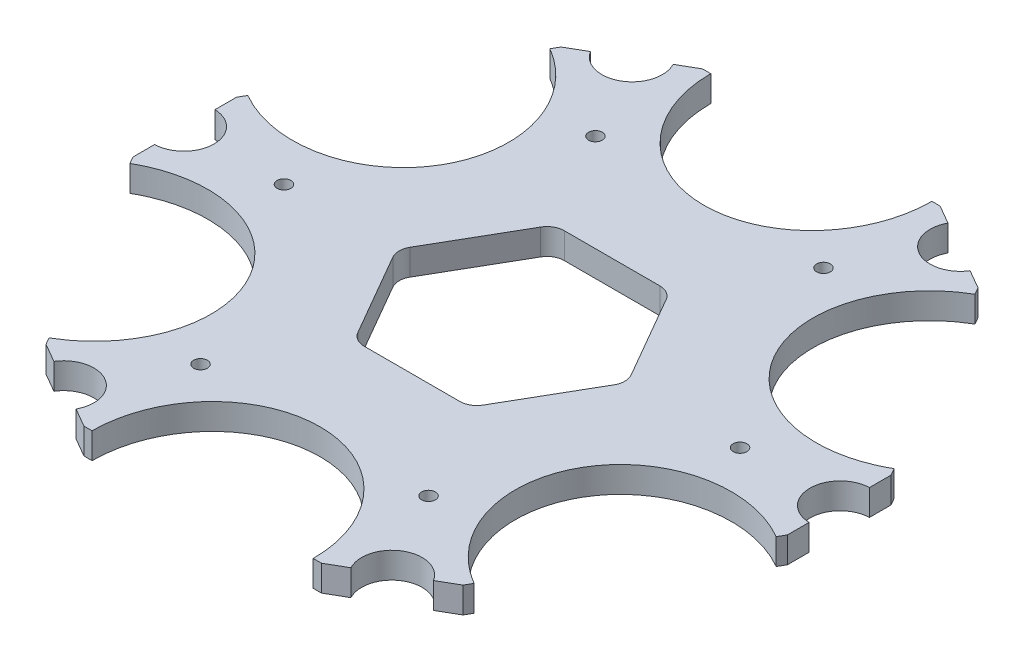
SolidWorks part; units mm, degrees
material "6061-T6 (SS)"
ref_plane "X-Y Datum" through (0, 0, 0) normal (0, 0, 1) x (1, 0, 0)
ref_plane "X-Z Datum" through (0, 0, 0) normal (0, 1, 0) x (1, 0, 0)
ref_plane "Y-Z Datum" through (0, 0, 0) normal (1, 0, 0) x (0, 0, -1)
sketch "Sketch1" plane through (0, 0, 0) normal (0, 1, 0) x (1, 0, 0)
  line L0 (-60.325, 0) -> (-60.325, -50000) construction
  line L1 (-60.1472, 5.5534) -> (-60.1472, 9.525)
  line L2 (-2.3269, 0) -> (49997.6731, 0) construction
  line L3 (0, 0) -> (-35355.3391, 35355.3391) construction
  line L4 (-60.1472, -5.5534) -> (-60.1472, -9.525)
  line L5 (-25.2642, 54.8657) -> (-21.8247, 56.8515)
  line L6 (-34.883, 49.3123) -> (-38.3225, 47.3265)
  line L7 (34.883, 49.3123) -> (38.3225, 47.3265)
  line L8 (25.2642, 54.8657) -> (21.8247, 56.8515)
  line L9 (60.1472, -5.5534) -> (60.1472, -9.525)
  line L10 (60.1472, 5.5534) -> (60.1472, 9.525)
  line L11 (25.2642, -54.8657) -> (21.8247, -56.8515)
  line L12 (34.883, -49.3123) -> (38.3225, -47.3265)
  line L13 (-34.883, -49.3123) -> (-38.3225, -47.3265)
  line L14 (-25.2642, -54.8657) -> (-21.8247, -56.8515)
  line L15 (-60.1472, 9.525) -> (-38.3225, 47.3265)
  line L16 (-21.8247, 56.8515) -> (21.8247, 56.8515)
  line L17 (38.3225, 47.3265) -> (60.1472, 9.525)
  line L18 (60.1472, -9.525) -> (38.3225, -47.3265)
  line L19 (21.8247, -56.8515) -> (-21.8247, -56.8515)
  line L20 (-38.3225, -47.3265) -> (-60.1472, -9.525)
  circle A0 centre (0, 0) radius 60.325 construction
  circle A1 centre (0, 0) radius 69.85 construction
  arc A2 (-60.1472, -5.5534) -> (-60.1472, 5.5534) centre (-60.325, 0) ccw
  arc A3 (-34.883, 49.3123) -> (-25.2642, 54.8657) centre (-30.1625, 52.243) ccw
  arc A4 (25.2642, 54.8657) -> (34.883, 49.3123) centre (30.1625, 52.243) ccw
  arc A5 (60.1472, 5.5534) -> (60.1472, -5.5534) centre (60.325, 0) ccw
  arc A6 (34.883, -49.3123) -> (25.2642, -54.8657) centre (30.1625, -52.243) ccw
  arc A7 (-25.2642, -54.8657) -> (-34.883, -49.3123) centre (-30.1625, -52.243) ccw
  circle A8 centre (0, 0) radius 12.7
  point P31 (0, 0)
  point P41 (0, 0)
  point P42 (0, 0)
  point P43 (0, 0)
  point P44 (0, 0)
  point P45 (0, 0)
  dimension "D1" = 120.65
  dimension "D2" = 139.7
  dimension "D7" = 25.4
  dimension "D8" = 5.5563
  dimension "D3" = 19.05
  dimension "D4" = 0.1778
  dimension "D5" = 45
extrude "Boss-Extrude1" add sketch "Sketch1" along normal mid plane 4.7625
sketch "Sketch2" plane through (0, 2.3813, 0) normal (0, 1, 0) x (1, 0, 0)
  line L1 (10.6172, -18.3896) -> (21.2345, 0)
  line L2 (21.2345, 0) -> (10.6172, 18.3896)
  line L3 (10.6172, 18.3896) -> (-10.6172, 18.3896)
  line L4 (-10.6172, 18.3896) -> (-21.2345, 0)
  line L5 (-21.2345, 0) -> (-10.6172, -18.3896)
  line L6 (-10.6172, -18.3896) -> (10.6172, -18.3896)
  circle A0 centre (0, 0) radius 18.3896 construction
  dimension "D1" = 36.7792
extrude "Cut-Extrude1" cut sketch "Sketch2" against normal through all
ref_axis "Wheel Axis" through (0, -2.6194, 0) along (0, 1, 0)
fillet "Fillet1" radius 3.175 6 edges at (-21.2345, 0, 0) (-10.6172, 0, -18.3896) (21.2345, 0, 0) (10.6172, 0, -18.3896) (-10.6172, 0, 18.3896) (10.6172, 0, 18.3896)
sketch "Sketch3" plane through (0, 2.3813, 0) normal (0, 1, 0) x (1, 0, 0)
  line L7 (-21.8247, -56.8515) -> (21.8247, -56.8515) construction
  ellipse E0 centre (0, -56.8515) end of major axis (0, -78.4415) minor radius 20.32
  dimension "D1" = 40.64
  dimension "D2" = 21.59
extrude "Cut-Extrude2" cut sketch "Sketch3" against normal through all
pattern_circular "CirPattern1" count 6 over 360 about axis through (0, -2.6194, 0) along (0, 1, 0) of "Cut-Extrude2"
sketch "Sketch4" plane through (0, 2.3813, 0) normal (0, 1, 0) x (1, 0, 0)
  circle A0 centre (41.91, 0) radius 1.27
  dimension "D1" = 41.91
extrude "Cut-Extrude3" cut sketch "Sketch4" against normal through all
sketch "Sketch5" plane through (0, 0, 0) normal (0, 0, 1) x (1, 0, 0)
  line L0 (0, 0) -> (0, 9.4144) construction
pattern_circular "CirPattern2" count 6 over 360 about axis through (0, 0, 0) along (0, 1, 0) of "Cut-Extrude3"
sketch "Sketch6" plane through (0, 2.3813, 0) normal (0, 1, 0) x (1, 0, 0)
  line L0 (11.5338, -16.8021) -> (20.3179, -1.5875) construction
  line L1 (-8.7842, -18.3896) -> (8.7842, -18.3896) construction
  line L2 (-20.3179, -1.5875) -> (-11.5338, -16.8021) construction
  line L3 (20.3179, 1.5875) -> (11.5338, 16.8021) construction
  line L4 (8.7842, 18.3896) -> (-8.7842, 18.3896) construction
  line L5 (-11.5338, 16.8021) -> (-20.3179, 1.5875) construction
  line L6 (11.5338, -16.8021) -> (20.3179, -1.5875)
  line L7 (-8.7842, -18.3896) -> (8.7842, -18.3896)
  line L8 (-20.3179, -1.5875) -> (-11.5338, -16.8021)
  line L9 (20.3179, 1.5875) -> (11.5338, 16.8021)
  line L10 (8.7842, 18.3896) -> (-8.7842, 18.3896)
  line L11 (-11.5338, 16.8021) -> (-20.3179, 1.5875)
  line L12 (-60.1472, -5.5534) -> (-60.1472, -9.525) construction
  line L13 (-60.1472, 9.525) -> (-60.1472, 5.5534) construction
  line L14 (-60.1472, -5.5534) -> (-60.1472, -9.525)
  line L15 (-60.1472, 9.525) -> (-60.1472, 5.5534)
  line L16 (-34.883, 49.3123) -> (-38.3225, 47.3265)
  line L17 (-21.8247, 56.8515) -> (-25.2642, 54.8657)
  line L18 (-22.2057, 57.5114) -> (-21.8247, 56.8515)
  line L19 (-22.2057, 57.5114) -> (-26.3336, 55.1282)
  line L20 (-34.5756, 50.3697) -> (-38.7035, 47.9864)
  line L21 (-38.7035, 47.9864) -> (-38.3225, 47.3265)
  line L22 (25.2642, 54.8657) -> (21.8247, 56.8515)
  line L23 (38.3225, 47.3265) -> (34.883, 49.3123)
  line L24 (38.7035, 47.9864) -> (38.3225, 47.3265)
  line L25 (38.7035, 47.9864) -> (34.5756, 50.3697)
  line L26 (26.3336, 55.1282) -> (22.2057, 57.5114)
  line L27 (22.2057, 57.5114) -> (21.8247, 56.8515)
  line L28 (60.1472, 5.5534) -> (60.1472, 9.525)
  line L29 (60.1472, -9.525) -> (60.1472, -5.5534)
  line L30 (60.9092, -9.525) -> (60.1472, -9.525)
  line L31 (60.9092, -9.525) -> (60.9092, -4.7585)
  line L32 (60.9092, 4.7585) -> (60.9092, 9.525)
  line L33 (60.9092, 9.525) -> (60.1472, 9.525)
  line L34 (34.883, -49.3123) -> (38.3225, -47.3265)
  line L35 (21.8247, -56.8515) -> (25.2642, -54.8657)
  line L36 (22.2057, -57.5114) -> (21.8247, -56.8515)
  line L37 (22.2057, -57.5114) -> (26.3336, -55.1282)
  line L38 (34.5756, -50.3697) -> (38.7035, -47.9864)
  line L39 (38.7035, -47.9864) -> (38.3225, -47.3265)
  line L40 (-25.2642, -54.8657) -> (-21.8247, -56.8515)
  line L41 (-38.3225, -47.3265) -> (-34.883, -49.3123)
  line L42 (-38.7035, -47.9864) -> (-38.3225, -47.3265)
  line L43 (-38.7035, -47.9864) -> (-34.5756, -50.3697)
  line L44 (-26.3336, -55.1282) -> (-22.2057, -57.5114)
  line L45 (-22.2057, -57.5114) -> (-21.8247, -56.8515)
  line L47 (-60.9092, 9.525) -> (-60.1472, 9.525)
  line L49 (19.658, 1.2065) -> (10.8739, 16.4211)
  line L50 (10.8739, -16.4211) -> (19.658, -1.2065)
  line L51 (-8.7842, -17.6276) -> (8.7842, -17.6276)
  line L52 (-19.658, -1.2065) -> (-10.8739, -16.4211)
  line L53 (-10.8739, 16.4211) -> (-19.658, 1.2065)
  line L54 (8.7842, 17.6276) -> (-8.7842, 17.6276)
  line L55 (19.658, 1.2065) -> (10.8739, 16.4211)
  line L56 (10.8739, -16.4211) -> (19.658, -1.2065)
  line L57 (-8.7842, -17.6276) -> (8.7842, -17.6276)
  line L58 (-19.658, -1.2065) -> (-10.8739, -16.4211)
  line L59 (-10.8739, 16.4211) -> (-19.658, 1.2065)
  line L60 (8.7842, 17.6276) -> (-8.7842, 17.6276)
  line L61 (-60.9092, 9.525) -> (-60.9092, 4.7585)
  line L62 (-60.9092, -4.7585) -> (-60.9092, -9.525)
  line L63 (-60.9092, 9.525) -> (-60.9092, 4.7585)
  line L64 (-60.9092, -4.7585) -> (-60.9092, -9.525)
  line L66 (-60.9092, -9.525) -> (-60.1472, -9.525)
  arc A0 (20.3179, -1.5875) -> (20.3179, 1.5875) centre (17.5683, 0) ccw construction
  arc A1 (8.7842, -18.3896) -> (11.5338, -16.8021) centre (8.7842, -15.2146) ccw construction
  arc A2 (-11.5338, -16.8021) -> (-8.7842, -18.3896) centre (-8.7842, -15.2146) ccw construction
  arc A3 (-20.3179, 1.5875) -> (-20.3179, -1.5875) centre (-17.5683, 0) ccw construction
  arc A4 (11.5338, 16.8021) -> (8.7842, 18.3896) centre (8.7842, 15.2146) ccw construction
  arc A5 (-8.7842, 18.3896) -> (-11.5338, 16.8021) centre (-8.7842, 15.2146) ccw construction
  arc A6 (20.3179, -1.5875) -> (20.3179, 1.5875) centre (17.5683, 0) ccw
  arc A7 (8.7842, -18.3896) -> (11.5338, -16.8021) centre (8.7842, -15.2146) ccw
  arc A8 (-11.5338, -16.8021) -> (-8.7842, -18.3896) centre (-8.7842, -15.2146) ccw
  arc A9 (-20.3179, 1.5875) -> (-20.3179, -1.5875) centre (-17.5683, 0) ccw
  arc A10 (11.5338, 16.8021) -> (8.7842, 18.3896) centre (8.7842, 15.2146) ccw
  arc A11 (-8.7842, 18.3896) -> (-11.5338, 16.8021) centre (-8.7842, 15.2146) ccw
  arc A12 (-60.1472, -5.5534) -> (-60.1472, 5.5534) centre (-60.325, 0) ccw construction
  arc A13 (-60.1472, -5.5534) -> (-60.1472, 5.5534) centre (-60.325, 0) ccw
  arc A14 (-34.883, 49.3123) -> (-25.2642, 54.8657) centre (-30.1625, 52.243) ccw
  arc A15 (-34.5756, 50.3697) -> (-26.3336, 55.1282) centre (-30.1625, 52.243) ccw
  arc A16 (25.2642, 54.8657) -> (34.883, 49.3123) centre (30.1625, 52.243) ccw
  arc A17 (26.3336, 55.1282) -> (34.5756, 50.3697) centre (30.1625, 52.243) ccw
  arc A18 (60.1472, 5.5534) -> (60.1472, -5.5534) centre (60.325, 0) ccw
  arc A19 (60.9092, 4.7585) -> (60.9092, -4.7585) centre (60.325, 0) ccw
  arc A20 (34.883, -49.3123) -> (25.2642, -54.8657) centre (30.1625, -52.243) ccw
  arc A21 (34.5756, -50.3697) -> (26.3336, -55.1282) centre (30.1625, -52.243) ccw
  arc A22 (-25.2642, -54.8657) -> (-34.883, -49.3123) centre (-30.1625, -52.243) ccw
  arc A23 (-26.3336, -55.1282) -> (-34.5756, -50.3697) centre (-30.1625, -52.243) ccw
  arc A38 (-60.9092, -4.7585) -> (-60.9092, 4.7585) centre (-60.325, 0) ccw
  arc A39 (-60.9092, -4.7585) -> (-60.9092, 4.7585) centre (-60.325, 0) ccw
  arc A41 (10.8739, 16.4211) -> (8.7842, 17.6276) centre (8.7842, 15.2146) ccw
  arc A42 (19.658, -1.2065) -> (19.658, 1.2065) centre (17.5683, 0) ccw
  arc A43 (8.7842, -17.6276) -> (10.8739, -16.4211) centre (8.7842, -15.2146) ccw
  arc A44 (-10.8739, -16.4211) -> (-8.7842, -17.6276) centre (-8.7842, -15.2146) ccw
  arc A45 (-19.658, 1.2065) -> (-19.658, -1.2065) centre (-17.5683, 0) ccw
  arc A46 (-8.7842, 17.6276) -> (-10.8739, 16.4211) centre (-8.7842, 15.2146) ccw
  arc A47 (10.8739, 16.4211) -> (8.7842, 17.6276) centre (8.7842, 15.2146) ccw
  arc A48 (19.658, -1.2065) -> (19.658, 1.2065) centre (17.5683, 0) ccw
  arc A49 (8.7842, -17.6276) -> (10.8739, -16.4211) centre (8.7842, -15.2146) ccw
  arc A50 (-10.8739, -16.4211) -> (-8.7842, -17.6276) centre (-8.7842, -15.2146) ccw
  arc A51 (-19.658, 1.2065) -> (-19.658, -1.2065) centre (-17.5683, 0) ccw
  arc A52 (-8.7842, 17.6276) -> (-10.8739, 16.4211) centre (-8.7842, 15.2146) ccw
  point P80 (0, 0)
  dimension "D1" = 0.762
  dimension "D2" = 0.762
  dimension "D3" = 6
extrude "Boss-Extrude2" [suppressed] add sketch "Sketch6" against normal up to surface (4.7625 mm away)
